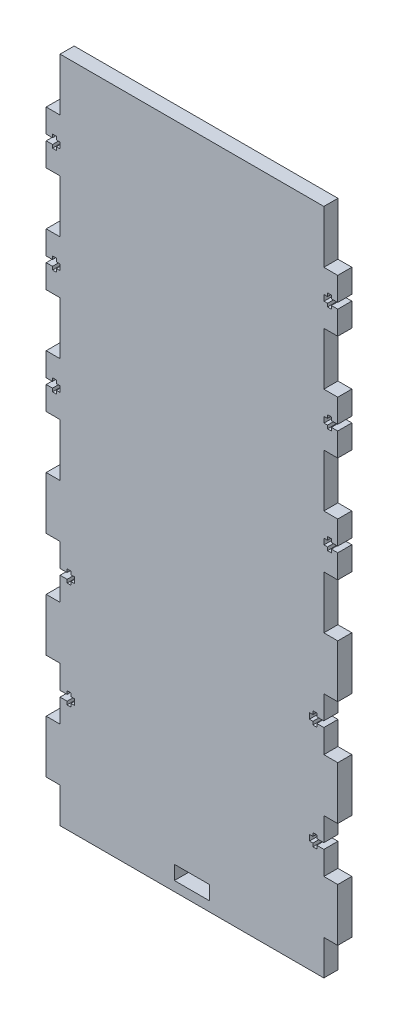
SolidWorks part; units mm, degrees
material "Acrylic (Medium-high impact)"
ref_plane "Front Plane" through (0, 0, 0) normal (0, 0, 1) x (1, 0, 0)
ref_plane "Top Plane" through (0, 0, 0) normal (0, 1, 0) x (1, 0, 0)
ref_plane "Right Plane" through (0, 0, 0) normal (1, 0, 0) x (0, 0, -1)
sketch "Sketch1" plane through (0, 0, 0) normal (0, 0, 1) x (1, 0, 0)
  line L1 (0, 0) -> (150, 0)
  line L2 (0, 0) -> (0, 380)
  line L3 (0, 380) -> (150, 380)
  line L4 (150, 0) -> (150, 380)
  line L5 (65, 13.5) -> (85, 13.5)
  line L6 (65, 13.5) -> (65, 5.5)
  line L7 (65, 5.5) -> (85, 5.5)
  line L8 (85, 13.5) -> (85, 5.5)
  dimension "D1" = 150
  dimension "D2" = 380
extrude "Boss-Extrude1" add sketch "Sketch1" along normal blind 8
sketch "Sketch2" plane through (0, 0, 8) normal (0, 0, 1) x (1, 0, 0)
  line L0 (150, 0) -> (150, 380) construction
  line L1 (150, 350) -> (157.9, 350)
  line L2 (150, 350) -> (150, 320)
  line L3 (150, 320) -> (157.9, 320)
  line L4 (157.9, 350) -> (157.9, 320)
  line L5 (150, 380) -> (0, 380) construction
  line L6 (-7.9, 350) -> (0, 350)
  line L7 (-7.9, 350) -> (-7.9, 320)
  line L8 (-7.9, 320) -> (0, 320)
  line L9 (0, 350) -> (0, 320)
  line L10 (150, 290) -> (157.9, 290)
  line L11 (150, 290) -> (150, 260)
  line L12 (150, 260) -> (157.9, 260)
  line L13 (157.9, 290) -> (157.9, 260)
  line L14 (-7.9, 290) -> (0, 290)
  line L15 (-7.9, 290) -> (-7.9, 260)
  line L16 (-7.9, 260) -> (0, 260)
  line L17 (0, 290) -> (0, 260)
  line L18 (150, 230) -> (157.9, 230)
  line L19 (150, 230) -> (150, 200)
  line L20 (150, 200) -> (157.9, 200)
  line L21 (157.9, 230) -> (157.9, 200)
  line L22 (75, 380) -> (75, 0) construction
  line L23 (0, 0) -> (150, 0) construction
  line L24 (-7.9, 230) -> (0, 230)
  line L25 (-7.9, 230) -> (-7.9, 200)
  line L26 (-7.9, 200) -> (0, 200)
  line L27 (0, 230) -> (0, 200)
  line L28 (150, 170) -> (157.9, 170)
  line L29 (150, 170) -> (150, 140)
  line L30 (150, 140) -> (157.9, 140)
  line L31 (157.9, 170) -> (157.9, 140)
  line L32 (-7.9, 170) -> (0, 170)
  line L33 (-7.9, 170) -> (-7.9, 140)
  line L34 (-7.9, 140) -> (0, 140)
  line L35 (0, 170) -> (0, 140)
  line L36 (150, 110) -> (157.9, 110)
  line L37 (150, 110) -> (150, 80)
  line L38 (150, 80) -> (157.9, 80)
  line L39 (157.9, 110) -> (157.9, 80)
  line L40 (-7.9, 110) -> (0, 110)
  line L41 (-7.9, 110) -> (-7.9, 80)
  line L42 (-7.9, 80) -> (0, 80)
  line L43 (0, 110) -> (0, 80)
  line L44 (150, 50) -> (157.9, 50)
  line L45 (150, 50) -> (150, 20)
  line L46 (150, 20) -> (157.9, 20)
  line L47 (157.9, 50) -> (157.9, 20)
  line L48 (-7.9, 50) -> (0, 50)
  line L49 (-7.9, 50) -> (-7.9, 20)
  line L50 (-7.9, 20) -> (0, 20)
  line L51 (0, 50) -> (0, 20)
  dimension "D1" = 7.9
  dimension "D2" = 30
  dimension "D3" = 30
  dimension "D4" = 2
extrude "Boss-Extrude2" add sketch "Sketch2" against normal blind 8
sketch "Sketch3" plane through (0, 0, 0) normal (0, 0, -1) x (-1, 0, 0)
  line L2 (7.9, 273.35) -> (7.9, 276.65)
  line L3 (-157.9, 335) -> (7.9, 335) construction
  line L4 (7.9, 276.65) -> (4.3, 276.65)
  line L5 (-150, 125) -> (0, 125) construction
  line L6 (4.3, 276.65) -> (4.3, 278.5)
  line L7 (-157.9, 320) -> (-157.9, 350) construction
  line L8 (4.3, 278.5) -> (2.1, 278.5)
  line L9 (7.9, 333.35) -> (7.9, 336.65)
  line L10 (7.9, 336.65) -> (4.3, 336.65)
  line L11 (4.3, 336.65) -> (4.3, 338.5)
  line L12 (4.3, 338.5) -> (2.1, 338.5)
  line L13 (2.1, 338.5) -> (2.1, 336.65)
  line L14 (2.1, 336.65) -> (0.1, 336.65)
  line L15 (0.1, 336.65) -> (0.1, 333.35)
  line L16 (2.1, 333.35) -> (0.1, 333.35)
  line L17 (2.1, 331.5) -> (2.1, 333.35)
  line L18 (4.3, 331.5) -> (2.1, 331.5)
  line L19 (4.3, 333.35) -> (4.3, 331.5)
  line L20 (7.9, 333.35) -> (4.3, 333.35)
  line L21 (2.1, 278.5) -> (2.1, 276.65)
  line L22 (2.1, 276.65) -> (0.1, 276.65)
  line L23 (0.1, 276.65) -> (0.1, 273.35)
  line L24 (2.1, 273.35) -> (0.1, 273.35)
  line L25 (2.1, 271.5) -> (2.1, 273.35)
  line L26 (4.3, 271.5) -> (2.1, 271.5)
  line L27 (4.3, 273.35) -> (4.3, 271.5)
  line L28 (7.9, 273.35) -> (4.3, 273.35)
  line L29 (-157.9, 275) -> (7.9, 275) construction
  line L30 (7.9, 213.35) -> (7.9, 216.65)
  line L31 (7.9, 216.65) -> (4.3, 216.65)
  line L32 (4.3, 216.65) -> (4.3, 218.5)
  line L33 (4.3, 218.5) -> (2.1, 218.5)
  line L34 (2.1, 218.5) -> (2.1, 216.65)
  line L35 (2.1, 216.65) -> (0.1, 216.65)
  line L36 (0.1, 216.65) -> (0.1, 213.35)
  line L37 (2.1, 213.35) -> (0.1, 213.35)
  line L38 (2.1, 211.5) -> (2.1, 213.35)
  line L39 (4.3, 211.5) -> (2.1, 211.5)
  line L40 (4.3, 213.35) -> (4.3, 211.5)
  line L41 (7.9, 213.35) -> (4.3, 213.35)
  line L42 (-157.9, 215) -> (7.9, 215) construction
  line L43 (-150, 110) -> (-150, 140) construction
  line L46 (-157.9, 213.35) -> (-154.3, 213.35)
  line L47 (-154.3, 213.35) -> (-154.3, 211.5)
  line L48 (-154.3, 211.5) -> (-152.1, 211.5)
  line L49 (-152.1, 211.5) -> (-152.1, 213.35)
  line L50 (-152.1, 213.35) -> (-150.1, 213.35)
  line L51 (-150.1, 216.65) -> (-150.1, 213.35)
  line L52 (-152.1, 216.65) -> (-150.1, 216.65)
  line L53 (-152.1, 218.5) -> (-152.1, 216.65)
  line L54 (-154.3, 218.5) -> (-152.1, 218.5)
  line L55 (-154.3, 216.65) -> (-154.3, 218.5)
  line L56 (-157.9, 216.65) -> (-154.3, 216.65)
  line L57 (-157.9, 213.35) -> (-157.9, 216.65)
  line L58 (-157.9, 273.35) -> (-154.3, 273.35)
  line L59 (-154.3, 273.35) -> (-154.3, 271.5)
  line L60 (-154.3, 271.5) -> (-152.1, 271.5)
  line L61 (-152.1, 271.5) -> (-152.1, 273.35)
  line L62 (-152.1, 273.35) -> (-150.1, 273.35)
  line L63 (-150.1, 276.65) -> (-150.1, 273.35)
  line L64 (-152.1, 276.65) -> (-150.1, 276.65)
  line L65 (-152.1, 278.5) -> (-152.1, 276.65)
  line L66 (-157.9, 333.35) -> (-154.3, 333.35)
  line L67 (-154.3, 333.35) -> (-154.3, 331.5)
  line L68 (-154.3, 331.5) -> (-152.1, 331.5)
  line L69 (-152.1, 331.5) -> (-152.1, 333.35)
  line L70 (-152.1, 333.35) -> (-150.1, 333.35)
  line L71 (-150.1, 336.65) -> (-150.1, 333.35)
  line L72 (-152.1, 336.65) -> (-150.1, 336.65)
  line L73 (-152.1, 338.5) -> (-152.1, 336.65)
  line L74 (-154.3, 338.5) -> (-152.1, 338.5)
  line L75 (-154.3, 336.65) -> (-154.3, 338.5)
  line L76 (-157.9, 336.65) -> (-154.3, 336.65)
  line L77 (-157.9, 333.35) -> (-157.9, 336.65)
  line L78 (-154.3, 278.5) -> (-152.1, 278.5)
  line L79 (-154.3, 276.65) -> (-154.3, 278.5)
  line L80 (-157.9, 276.65) -> (-154.3, 276.65)
  line L81 (-157.9, 273.35) -> (-157.9, 276.65)
  line L82 (0, 140) -> (0, 110) construction
  line L83 (0, 123.35) -> (0, 126.65)
  line L85 (0, 126.65) -> (-4, 126.65)
  line L86 (-4, 126.65) -> (-4, 128.5)
  line L87 (-4, 128.5) -> (-6.2, 128.5)
  line L88 (-6.2, 128.5) -> (-6.2, 126.65)
  line L90 (-6.2, 126.65) -> (-8.2, 126.65)
  line L91 (-8.2, 126.65) -> (-8.2, 123.35)
  line L92 (-6.2, 123.35) -> (-8.2, 123.35)
  line L93 (-6.2, 121.5) -> (-6.2, 123.35)
  line L94 (-4, 121.5) -> (-6.2, 121.5)
  line L95 (-4, 123.35) -> (-4, 121.5)
  line L96 (0, 123.35) -> (-4, 123.35)
  line L97 (0, 63.35) -> (0, 66.65)
  line L98 (0, 66.65) -> (-4, 66.65)
  line L99 (-4, 66.65) -> (-4, 68.5)
  line L100 (-4, 68.5) -> (-6.2, 68.5)
  line L101 (-6.2, 68.5) -> (-6.2, 66.65)
  line L102 (-6.2, 66.65) -> (-8.2, 66.65)
  line L103 (-8.2, 66.65) -> (-8.2, 63.35)
  line L104 (-6.2, 63.35) -> (-8.2, 63.35)
  line L105 (-6.2, 61.5) -> (-6.2, 63.35)
  line L106 (-4, 61.5) -> (-6.2, 61.5)
  line L107 (-4, 63.35) -> (-4, 61.5)
  line L108 (0, 63.35) -> (-4, 63.35)
  line L109 (-75, 380) -> (-75, 0) construction
  line L110 (-150, 380) -> (0, 380) construction
  line L111 (0, 0) -> (-150, 0) construction
  line L112 (-150, 63.35) -> (-146, 63.35)
  line L113 (-146, 63.35) -> (-146, 61.5)
  line L114 (-146, 61.5) -> (-143.8, 61.5)
  line L117 (-143.8, 61.5) -> (-143.8, 63.35)
  line L118 (-143.8, 63.35) -> (-141.8, 63.35)
  line L119 (-141.8, 66.65) -> (-141.8, 63.35)
  line L120 (-143.8, 66.65) -> (-141.8, 66.65)
  line L121 (-143.8, 68.5) -> (-143.8, 66.65)
  line L122 (-146, 68.5) -> (-143.8, 68.5)
  line L123 (-146, 66.65) -> (-146, 68.5)
  line L124 (-150, 66.65) -> (-146, 66.65)
  line L125 (-150, 63.35) -> (-150, 66.65)
  line L126 (-150, 123.35) -> (-146, 123.35)
  line L127 (-146, 123.35) -> (-146, 121.5)
  line L128 (-146, 121.5) -> (-143.8, 121.5)
  line L129 (-143.8, 121.5) -> (-143.8, 123.35)
  line L130 (-143.8, 123.35) -> (-141.8, 123.35)
  line L131 (-141.8, 126.65) -> (-141.8, 123.35)
  line L132 (-143.8, 126.65) -> (-141.8, 126.65)
  line L133 (-143.8, 128.5) -> (-143.8, 126.65)
  line L134 (-146, 128.5) -> (-143.8, 128.5)
  line L135 (-146, 126.65) -> (-146, 128.5)
  line L136 (-150, 126.65) -> (-146, 126.65)
  line L137 (-150, 123.35) -> (-150, 126.65)
  point P91 (-8.2, 125)
  point P109 (-8.2, 65)
  point P142 (-141.8, 65)
  point P143 (-141.8, 125)
  dimension "D2" = 2.2
  dimension "D1" = 4
  dimension "D3" = 2.2
  dimension "D4" = 2
  dimension "D5" = 2
  dimension "D6" = 7
  dimension "D7" = 3.3
  dimension "D8" = 3.3
  dimension "D9" = 7
  dimension "D10" = 2
extrude "Cut-Extrude2" cut sketch "Sketch3" against normal through all
